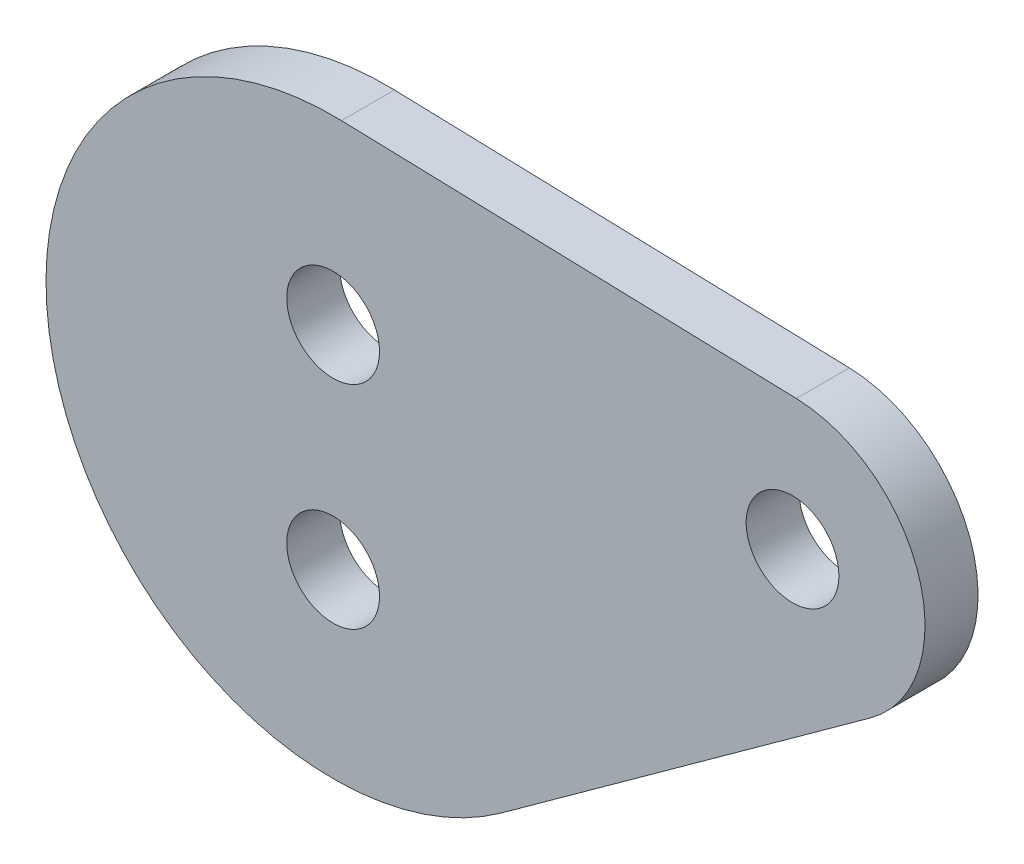
SolidWorks part; units mm, degrees
ref_plane "Plane1" through (0, 0, 0) normal (0, 0, 1) x (1, 0, 0)
ref_plane "Plane2" through (0, 0, 0) normal (0, 1, 0) x (1, 0, 0)
ref_plane "Plane3" through (0, 0, 0) normal (1, 0, 0) x (0, 0, -1)
sketch "Sketch1" plane through (0, 0, 0) normal (0, 0, 1) x (1, 0, 0)
  line L0 (0, 0) -> (46, 0) construction
  line L1 (0.9417, 32.4864) -> (52.4346, 30.9937)
  line L2 (60.7883, 3.8441) -> (19.0414, -26.3377)
  arc A0 (0.9417, 32.4864) -> (19.0414, -26.3377) centre (0, 0) ccw
  circle A1 centre (0, 12) radius 5.25
  circle A2 centre (0, -12) radius 5.25
  circle A3 centre (52, 16) radius 5.25
  arc A4 (60.7883, 3.8441) -> (52.4346, 30.9937) centre (52, 16) ccw
  dimension "D2" = 10.5
  dimension "D5" = 32.5
  dimension "D6" = 15
  dimension "D1" = 24
  dimension "D3" = 16
  dimension "D4" = 52
  dimension "D7" = 54.4059
extrude "Extrude1" add sketch "Sketch1" along normal blind 6
